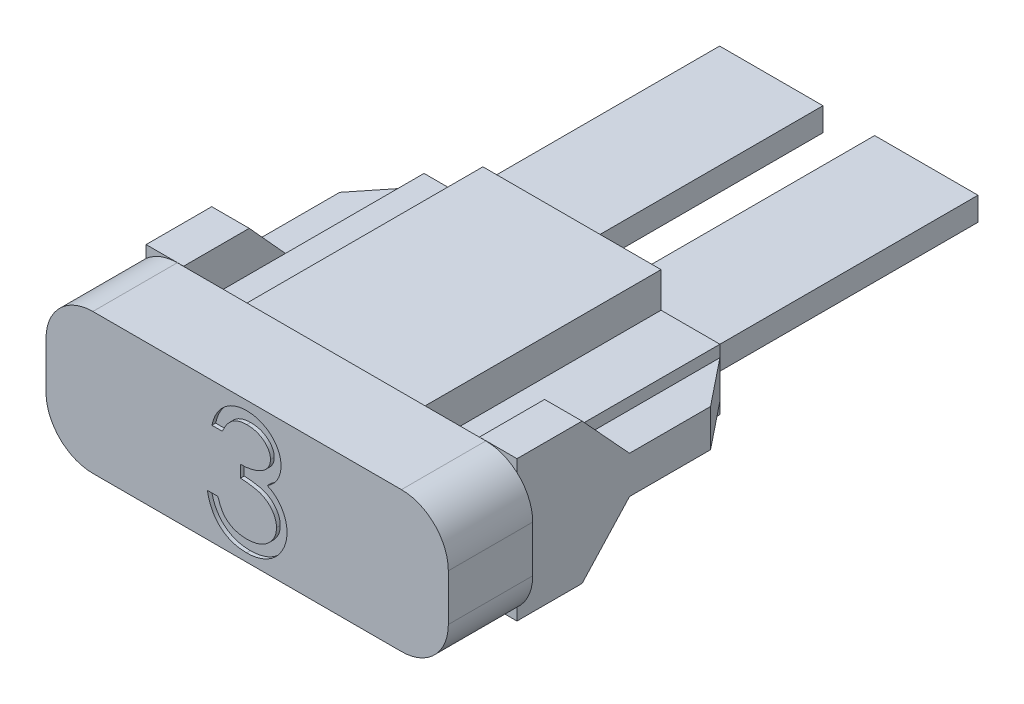
SolidWorks part; units mm, degrees
ref_plane "Front Plane" through (0, 0, 0) normal (0, 0, 1) x (1, 0, 0)
ref_plane "Top Plane" through (0, 0, 0) normal (0, 1, 0) x (1, 0, 0)
ref_plane "Right Plane" through (0, 0, 0) normal (1, 0, 0) x (0, 0, -1)
sketch "Sketch1" plane through (0, 0, 0) normal (0, 0, 1) x (1, 0, 0)
  line L1 (1.27, 0) -> (9.63, 0)
  line L2 (0, 1.27) -> (0, 2.53)
  line L3 (1.27, 3.8) -> (9.63, 3.8)
  line L4 (10.9, 1.27) -> (10.9, 2.53)
  arc A0 (0, 2.53) -> (1.27, 3.8) centre (1.27, 2.53) cw
  arc A1 (1.27, 0) -> (0, 1.27) centre (1.27, 1.27) cw
  arc A2 (10.9, 1.27) -> (9.63, 0) centre (9.63, 1.27) cw
  arc A3 (9.63, 3.8) -> (10.9, 2.53) centre (9.63, 2.53) cw
  point P8 (0, 0)
  dimension "D3" = 1.27
  dimension "D1" = 3.8
  dimension "D2" = 10.9
extrude "Extrude1" add sketch "Sketch1" along normal blind 2.286
sketch "Sketch2" plane through (0, 0, 0) normal (0, 0, -1) x (-1, 0, 0)
  line L0 (-3.545, 1.5825) -> (-3.545, 0.63)
  line L1 (-8.95, 2.2175) -> (-7.355, 2.2175)
  line L2 (-8.95, 2.2175) -> (-8.95, 1.5825)
  line L3 (-8.95, 1.5825) -> (-7.355, 1.5825)
  line L4 (-7.355, 1.5825) -> (-7.355, 0.63)
  line L5 (-7.355, 3.17) -> (-3.545, 3.17)
  line L6 (-7.355, 3.17) -> (-7.355, 2.2175)
  line L7 (-7.355, 0.63) -> (-3.545, 0.63)
  line L8 (-3.545, 3.17) -> (-3.545, 2.2175)
  line L9 (-3.545, 2.2175) -> (-1.95, 2.2175)
  line L10 (-7.863, 3.678) -> (-7.863, 2.7255)
  line L11 (-3.545, 1.5825) -> (-1.95, 1.5825)
  line L12 (-1.95, 2.2175) -> (-1.95, 1.5825)
  line L13 (-9.458, 2.7255) -> (-7.863, 2.7255)
  line L14 (-9.458, 2.7255) -> (-9.458, 1.0745)
  line L15 (-9.458, 1.0745) -> (-7.863, 1.0745)
  line L16 (-7.863, 1.0745) -> (-7.863, 0.122)
  line L17 (-7.863, 0.122) -> (-3.037, 0.122)
  line L18 (-3.037, 1.0745) -> (-3.037, 0.122)
  line L19 (-3.037, 1.0745) -> (-1.442, 1.0745)
  line L20 (-1.442, 2.7255) -> (-1.442, 1.0745)
  line L21 (-3.037, 2.7255) -> (-1.442, 2.7255)
  line L22 (-3.037, 3.678) -> (-3.037, 2.7255)
  line L23 (-7.863, 3.678) -> (-3.037, 3.678)
  line L25 (-1.27, 0) -> (-9.63, 0) construction
  line L27 (0, 2.53) -> (0, 1.27) construction
  line L28 (-5.45, 0.63) -> (-5.45, 0) construction
  line L29 (-1.27, 0) -> (-9.63, 0) construction
  line L30 (-1.442, 1.9) -> (0, 1.9) construction
  line L31 (0, 2.53) -> (0, 1.27) construction
  dimension "D1" = 0.635
  dimension "D2" = 2.54
  dimension "D3" = 0.9525
  dimension "D6" = 0.122
  dimension "D8" = 7
  dimension "D9" = 3.81
  dimension "D11" = 1.595
  dimension "D12" = 1.442
  dimension "D4" = 0.508
extrude "Extrude2" add sketch "Sketch2" along normal blind 6.514
sketch "Sketch3" plane through (1.442, 0, 0) normal (-1, 0, 0) x (0, 0, 1)
  line L0 (-6.514, 1.0745) -> (-6.514, 2.7255) construction
  line L1 (-6.514, 2.408) -> (-3.048, 2.408)
  line L2 (-6.514, 2.408) -> (-6.514, 1.392)
  line L3 (-6.514, 1.392) -> (-3.048, 1.392)
  line L5 (0, 2.53) -> (0, 1.27) construction
  line L6 (-1.778, 3.805) -> (0, 3.805)
  line L8 (-1.778, -0.005) -> (0, -0.005)
  line L9 (0, 3.805) -> (0, -0.005)
  line L10 (-6.514, 2.7255) -> (0, 2.7255) construction
  line L11 (-6.514, 1.0745) -> (0, 1.0745) construction
  line L12 (-1.778, 3.805) -> (-3.048, 2.408)
  line L13 (-3.048, 1.392) -> (-1.778, -0.005)
  dimension "D1" = 1.016
  dimension "D2" = 0.3175
  dimension "D3" = 0.3175
  dimension "D4" = 3.81
  dimension "D5" = 1.397
  dimension "D6" = 1.397
  dimension "D7" = 1.27
  dimension "D8" = 1.778
extrude "Extrude3" add sketch "Sketch3" along normal blind 1.016
sketch "Sketch4" plane through (9.458, 0, 0) normal (1, 0, 0) x (0, 0, -1)
  line L0 (6.514, 2.7255) -> (6.514, 1.0745) construction
  line L1 (3.048, 2.408) -> (6.514, 2.408)
  line L2 (3.048, 1.392) -> (2.7594, 1.0745) construction
  line L3 (3.048, 1.392) -> (6.514, 1.392)
  line L4 (6.514, 2.408) -> (6.514, 1.392)
  line L6 (0, 3.805) -> (1.764, 3.805)
  line L7 (0, 3.805) -> (0, -0.005)
  line L8 (0, -0.005) -> (1.764, -0.005)
  line L10 (1.764, 3.805) -> (3.048, 2.408)
  line L11 (1.764, -0.005) -> (3.048, 1.392)
  line L12 (6.514, 2.7255) -> (0, 2.7255) construction
  line L14 (0, 2.53) -> (0, 3.8) construction
  dimension "D1" = 1.016
  dimension "D2" = 0.3175
  dimension "D3" = 1.397
  dimension "D4" = 3.81
  dimension "D5" = 4.75
extrude "Extrude4" add sketch "Sketch4" along normal blind 1.016
chamfer "Chamfer1" distance 1.016 distance2 1.27 2 edges at (0.426, 1.9, -6.514) (10.474, 1.9, -6.514)
sketch "Sketch8" plane through (0, 1.5825, 0) normal (0, 1, 0) x (-1, 0, 0)
  line L1 (-1.95, 0) -> (-4.75, 0)
  line L2 (-1.95, 0) -> (-1.95, -14.014)
  line L3 (-1.95, -14.014) -> (-4.75, -14.014)
  line L5 (-8.95, 0) -> (-6.15, 0)
  line L6 (-8.95, 0) -> (-8.95, -14.014)
  line L7 (-8.95, -14.014) -> (-6.15, -14.014)
  line L10 (-1.442, -6.514) -> (-3.037, -6.514) construction
  line L11 (-7.863, -6.514) -> (-9.458, -6.514) construction
  line L23 (-6.15, 0) -> (-6.15, -14.014)
  line L24 (-4.75, 0) -> (-4.75, -14.014)
  line L25 (-1.442, 0) -> (-9.458, 0) construction
  dimension "D1" = 7.5
  dimension "D2" = 7.5
  dimension "D9" = 2.8
extrude "Blade" add sketch "Sketch8" along normal up to surface (0.635 mm away) up to face at (2.7475, 2.2175, -3.257)
sketch "Sketch5" plane through (0, 0, 2.286) normal (0, 0, 1) x (1, 0, 0)
  line L0 (0, 2.53) -> (0, 1.27) construction
  line L1 (1.27, 0) -> (9.63, 0) construction
  text T0 "10" font "Century Gothic" height in points 12
  dimension "D1" = 6.7818
  dimension "D2" = 0.9525
extrude "\"10\"" [suppressed] cut sketch "Sketch5" against normal blind 0.1016
sketch "Sketch6" [suppressed] plane through (0, 0, 2.286) normal (0, 0, 1) x (1, 0, 0)
  line L0 (1.27, 0) -> (17.78, 0) construction
  line L1 (0, 3.81) -> (0, 1.27) construction
  text T0 "40" font "Century Gothic" height in points 12
  dimension "D1" = 1.016
  dimension "D2" = 6.985
extrude "\"40\"" [suppressed] cut sketch "Sketch6" against normal blind 0.1016
sketch "Sketch7" [suppressed] plane through (0, 0, 2.286) normal (0, 0, 1) x (1, 0, 0)
  line L0 (1.27, 0) -> (17.78, 0) construction
  line L1 (0, 3.81) -> (0, 1.27) construction
  text T0 "30" font "Century Gothic" height in points 12
  dimension "D1" = 1.016
  dimension "D2" = 6.985
extrude "\"30\"" [suppressed] cut sketch "Sketch7" against normal blind 0.1016
sketch "Sketch9" [suppressed] plane through (0, 0, 2.286) normal (0, 0, 1) x (1, 0, 0)
  line L0 (1.27, 0) -> (17.78, 0) construction
  line L1 (0, 3.81) -> (0, 1.27) construction
  text T0 "7.5" font "Century Gothic" height in points 12
  dimension "D1" = 1.016
  dimension "D2" = 6.604
extrude "\"7.5\"" [suppressed] cut sketch "Sketch9" against normal blind 0.1016
sketch "Sketch10" [suppressed] plane through (0, 0, 2.286) normal (0, 0, 1) x (1, 0, 0)
  line L0 (1.27, 0) -> (17.78, 0) construction
  line L1 (0, 3.81) -> (0, 1.27) construction
  text T0 "1" font "Century Gothic" height in points 12
  dimension "D1" = 1.016
  dimension "D2" = 8.255
extrude "\"1\"" [suppressed] cut sketch "Sketch10" against normal blind 0.1016
sketch "Sketch11" [suppressed] plane through (0, 0, 2.286) normal (0, 0, 1) x (1, 0, 0)
  line L0 (1.27, 0) -> (17.78, 0) construction
  line L1 (0, 3.81) -> (0, 1.27) construction
  text T0 "15" font "Century Gothic" height in points 12
  dimension "D1" = 1.016
  dimension "D2" = 6.858
extrude "\"15\"" [suppressed] cut sketch "Sketch11" against normal blind 0.1016
sketch "Sketch12" [suppressed] plane through (0, 0, 2.286) normal (0, 0, 1) x (1, 0, 0)
  line L0 (1.27, 0) -> (17.78, 0) construction
  line L1 (0, 3.81) -> (0, 1.27) construction
  text T0 "2" font "Century Gothic" height in points 12
  dimension "D1" = 1.016
  dimension "D2" = 8.255
extrude "\"2\"" [suppressed] cut sketch "Sketch12" against normal blind 0.1016
sketch "Sketch13" [suppressed] plane through (0, 0, 2.286) normal (0, 0, 1) x (1, 0, 0)
  line L0 (1.27, 0) -> (17.78, 0) construction
  line L1 (0, 3.81) -> (0, 1.27) construction
  text T0 "20" font "Century Gothic" height in points 12
  dimension "D1" = 1.016
  dimension "D2" = 6.985
extrude "\"20\"" [suppressed] cut sketch "Sketch13" against normal blind 0.1016
sketch "Sketch14" [suppressed] plane through (0, 0, 2.286) normal (0, 0, 1) x (1, 0, 0)
  line L0 (1.27, 0) -> (17.78, 0) construction
  line L1 (0, 3.81) -> (0, 1.27) construction
  text T0 "25" font "Century Gothic" height in points 12
  dimension "D1" = 1.016
  dimension "D2" = 6.985
extrude "\"25\"" [suppressed] cut sketch "Sketch14" against normal blind 0.1016
sketch "Sketch15" plane through (0, 0, 2.286) normal (0, 0, 1) x (1, 0, 0)
  line L0 (1.27, 0) -> (9.63, 0) construction
  line L1 (0, 2.53) -> (0, 1.27) construction
  text T0 "3" font "Century Gothic" height in points 12
  dimension "D1" = 0.3
  dimension "D2" = 4.25
extrude "\"3\"" cut sketch "Sketch15" against normal blind 0.1016
sketch "Sketch16" [suppressed] plane through (0, 0, 2.286) normal (0, 0, 1) x (1, 0, 0)
  line L0 (1.27, 0) -> (17.78, 0) construction
  line L1 (0, 3.81) -> (0, 1.27) construction
  text T0 "4" font "Century Gothic" height in points 12
  dimension "D1" = 1.016
  dimension "D2" = 8.255
extrude "\"4\"" [suppressed] cut sketch "Sketch16" against normal blind 0.1016
sketch "Sketch17" [suppressed] plane through (0, 0, 2.286) normal (0, 0, 1) x (1, 0, 0)
  line L0 (1.27, 0) -> (17.78, 0) construction
  line L1 (0, 3.81) -> (0, 1.27) construction
  text T0 "5" font "Century Gothic" height in points 12
  dimension "D1" = 1.016
  dimension "D2" = 8.255
extrude "\"5\"" [suppressed] cut sketch "Sketch17" against normal blind 0.1016
